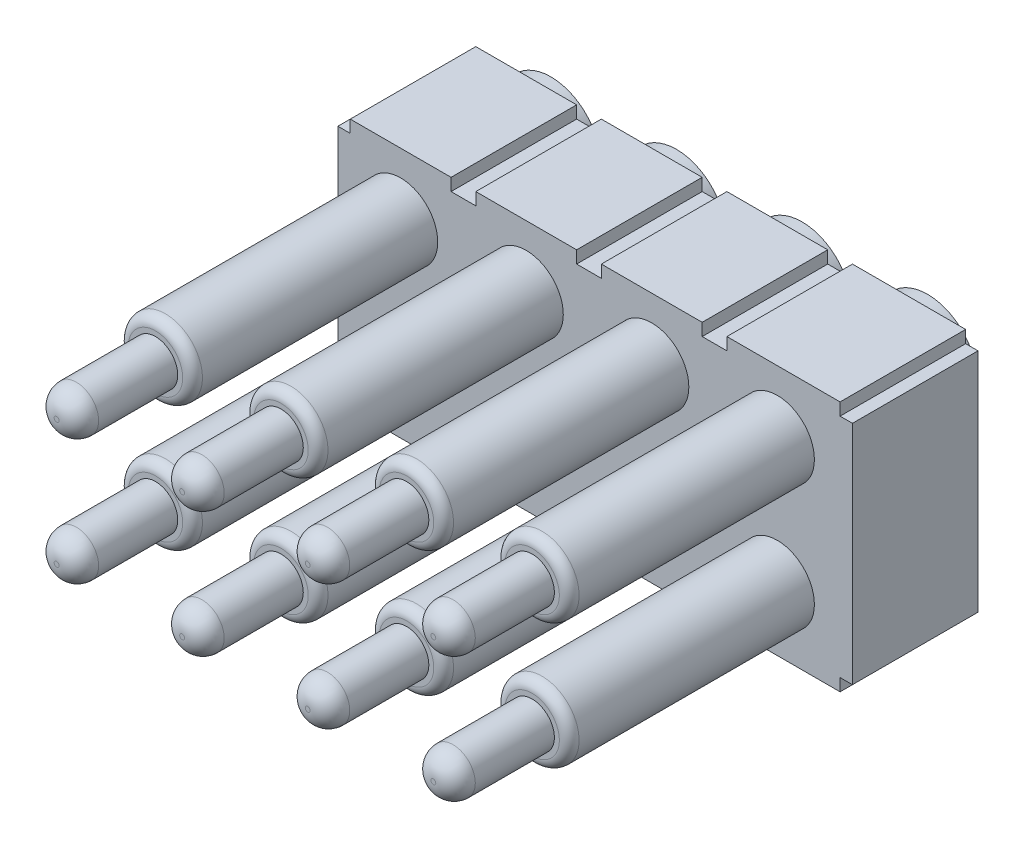
SolidWorks part; units mm, degrees
ref_plane "前视基准面" through (0, 0, 0) normal (0, 0, 1) x (1, 0, 0)
ref_plane "上视基准面" through (0, 0, 0) normal (0, 1, 0) x (1, 0, 0)
ref_plane "右视基准面" through (0, 0, 0) normal (1, 0, 0) x (0, 0, -1)
sketch "草图1" plane through (0, 0, 0) normal (0, 0, 1) x (1, 0, 0)
  line L0 (5.08, 2.29) -> (5.08, 2.54)
  line L1 (5.33, 0) -> (5.33, 2.29)
  line L2 (5.08, 2.54) -> (2.79, 2.54)
  line L3 (-5.08, 2.29) -> (-5.08, -2.29)
  line L4 (-4.83, -2.54) -> (-2.79, -2.54)
  line L5 (5.33, -2.29) -> (5.33, 0)
  line L7 (0.25, 2.54) -> (0.25, 2.29)
  line L8 (0.25, 2.29) -> (-0.25, 2.29)
  line L9 (-0.25, 2.29) -> (-0.25, 2.54)
  line L10 (-2.29, 2.54) -> (-2.29, 2.29)
  line L11 (-2.29, 2.29) -> (-2.79, 2.29)
  line L12 (-2.79, 2.29) -> (-2.79, 2.54)
  line L13 (-4.83, 2.54) -> (-4.83, 2.29)
  line L14 (-4.83, 2.29) -> (-5.08, 2.29)
  line L17 (2.79, 2.54) -> (2.79, 2.29)
  line L18 (2.79, 2.29) -> (2.29, 2.29)
  line L19 (2.29, 2.29) -> (2.29, 2.54)
  line L20 (2.29, 2.54) -> (0.25, 2.54)
  line L21 (5.33, 2.29) -> (5.08, 2.29)
  line L23 (0.25, 2.54) -> (2.29, 2.54) construction
  line L24 (2.79, -2.54) -> (5.08, -2.54)
  line L25 (0.25, -2.54) -> (2.29, -2.54)
  line L26 (5.33, -2.29) -> (5.08, -2.29)
  line L27 (5.08, -2.29) -> (5.08, -2.54)
  line L28 (2.79, -2.54) -> (2.79, -2.29)
  line L29 (2.79, -2.29) -> (2.29, -2.29)
  line L30 (2.29, -2.29) -> (2.29, -2.54)
  line L31 (0.25, -2.54) -> (0.25, -2.29)
  line L32 (0.25, -2.29) -> (-0.25, -2.29)
  line L33 (-0.25, -2.29) -> (-0.25, -2.54)
  line L34 (-2.29, -2.54) -> (-2.29, -2.29)
  line L35 (-2.29, -2.29) -> (-2.79, -2.29)
  line L36 (-2.79, -2.29) -> (-2.79, -2.54)
  line L37 (-4.83, -2.54) -> (-4.83, -2.29)
  line L39 (-4.83, -2.29) -> (-5.08, -2.29)
  line L40 (-2.29, -2.54) -> (-0.25, -2.54)
  line L41 (5.33, 2.54) -> (5.33, 2.29) [skipped]
  line L42 (-2.79, 2.54) -> (-4.83, 2.54)
  line L43 (-0.25, 2.54) -> (-2.29, 2.54)
  line L44 (-0.25, 2.54) -> (-2.29, 2.54) construction
  line L45 (-5.33, 2.29) -> (-5.33, 2.54) [skipped]
  line L46 (4.83, 2.29) -> (4.83, 2.54) [skipped]
  dimension "D1" = 3
  dimension "D3" = 3
extrude "凸台-拉伸1" add sketch "草图1" along normal blind 2.54
sketch "草图2" plane through (0, 0, 0) normal (0, 0, -1) x (-1, 0, 0)
  circle A0 centre (-1.27, 1.27) radius 1
  circle A1 centre (1.27, 1.27) radius 1
  circle A2 centre (3.81, 1.27) radius 1
  circle A3 centre (1.27, -1.27) radius 1
  circle A4 centre (3.81, -1.27) radius 1
  circle A5 centre (-1.27, -1.27) radius 1
  circle A6 centre (-3.81, 1.27) radius 1
  circle A7 centre (-3.81, -1.27) radius 1
  dimension "D1" = 3
  dimension "D2" = 2
extrude "凸台-拉伸2" add sketch "草图2" along normal blind 0.5
sketch "草图3" plane through (0, 0, -0.5) normal (0, 0, -1) x (-1, 0, 0)
  circle A0 centre (-3.81, 1.27) radius 0.75
  circle A1 centre (-1.27, 1.27) radius 0.75
  circle A2 centre (1.27, 1.27) radius 0.75
  circle A3 centre (3.81, 1.27) radius 0.75
  circle A4 centre (-1.27, -1.27) radius 0.75
  circle A5 centre (1.27, -1.27) radius 0.75
  circle A6 centre (3.81, -1.27) radius 0.75
  circle A7 centre (-3.81, -1.27) radius 0.75
  dimension "D1" = 4
  dimension "D2" = 2
extrude "凸台-拉伸3" add sketch "草图3" against normal blind 8
sketch "草图4" plane through (0, 0, 7.5) normal (0, 0, 1) x (1, 0, 0)
  circle A0 centre (-3.81, 1.27) radius 0.45
  circle A1 centre (-1.27, 1.27) radius 0.45
  circle A2 centre (1.27, 1.27) radius 0.45
  circle A3 centre (3.81, 1.27) radius 0.45
  circle A4 centre (-1.27, -1.27) radius 0.45
  circle A5 centre (1.27, -1.27) radius 0.45
  circle A6 centre (3.81, -1.27) radius 0.45
  circle A7 centre (-3.81, -1.27) radius 0.45
  dimension "D1" = 4
  dimension "D2" = 2
extrude "凸台-拉伸4" add sketch "草图4" along normal blind 2
fillet "圆角1" radius 0.4 8 edges at (4.26, 1.27, 9.5) (-3.36, -1.27, 9.5) (-3.36, 1.27, 9.5) (-0.82, 1.27, 9.5) (-0.82, -1.27, 9.5) (1.72, -1.27, 9.5) (1.72, 1.27, 9.5) (4.26, -1.27, 9.5)
fillet "圆角2" radius 0.2 8 edges at (-4.56, 1.27, 7.5) (-2.02, -1.27, 7.5) (-2.02, 1.27, 7.5) (0.52, 1.27, 7.5) (0.52, -1.27, 7.5) (3.06, 1.27, 7.5) (3.06, -1.27, 7.5) (-4.56, -1.27, 7.5)
sketch "草图5" plane through (0, 0, -0.5) normal (0, 0, -1) x (-1, 0, 0)
  circle A0 centre (0, 0) radius 0.6261
